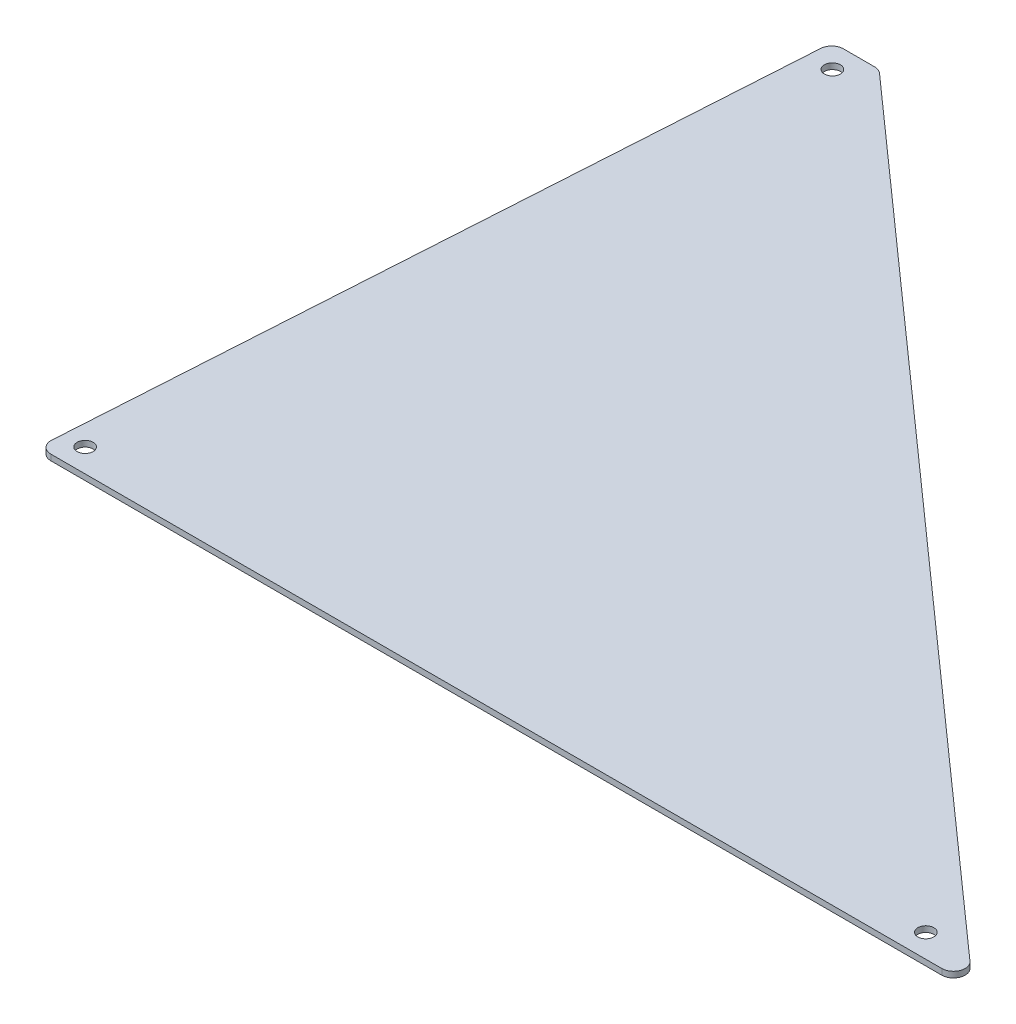
SolidWorks part; units mm, degrees
ref_plane "Front Plane" through (0, 0, 0) normal (0, 0, 1) x (1, 0, 0)
ref_plane "Top Plane" through (0, 0, 0) normal (0, 1, 0) x (1, 0, 0)
ref_plane "Right Plane" through (0, 0, 0) normal (1, 0, 0) x (0, 0, -1)
sketch "Sketch1" plane through (0, 0, 0) normal (0, 1, 0) x (1, 0, 0)
  line L0 (3.3796, 0) -> (245.6491, 0)
  line L1 (247.7585, 5.548) -> (26.3022, 202.398)
  line L2 (24.1929, 203.2) -> (15.6828, 203.2)
  line L3 (12.5139, 200.2231) -> (0.2108, 3.3731)
  circle A0 centre (234.95, 6.35) radius 2.1828
  circle A1 centre (6.35, 6.35) radius 2.1828
  circle A2 centre (19.05, 196.85) radius 2.1828
  arc A3 (0.2108, 3.3731) -> (3.3796, 0) centre (3.3796, 3.175) ccw
  arc A4 (245.6491, 0) -> (247.7585, 5.548) centre (245.6491, 3.175) ccw
  arc A5 (26.3022, 202.398) -> (24.1929, 203.2) centre (24.1929, 200.025) ccw
  arc A6 (15.6828, 203.2) -> (12.5139, 200.2231) centre (15.6828, 200.025) ccw
  point P13 (0, 0)
  point P16 (254, 0)
  point P19 (25.4, 203.2)
  point P22 (12.7, 203.2)
  dimension "D6" = 4.3656
  dimension "D10" = 4.3656
  dimension "D13" = 4.3656
  dimension "D14" = 3.175
  dimension "D1" = 254
  dimension "D2" = 203.2
  dimension "D3" = 12.7
  dimension "D4" = 12.7
  dimension "D5" = 6.35
  dimension "D7" = 19.05
  dimension "D8" = 6.35
  dimension "D9" = 6.35
  dimension "D11" = 6.35
  dimension "D12" = 6.35
extrude "Boss-Extrude1" add sketch "Sketch1" along normal blind 1.5875
